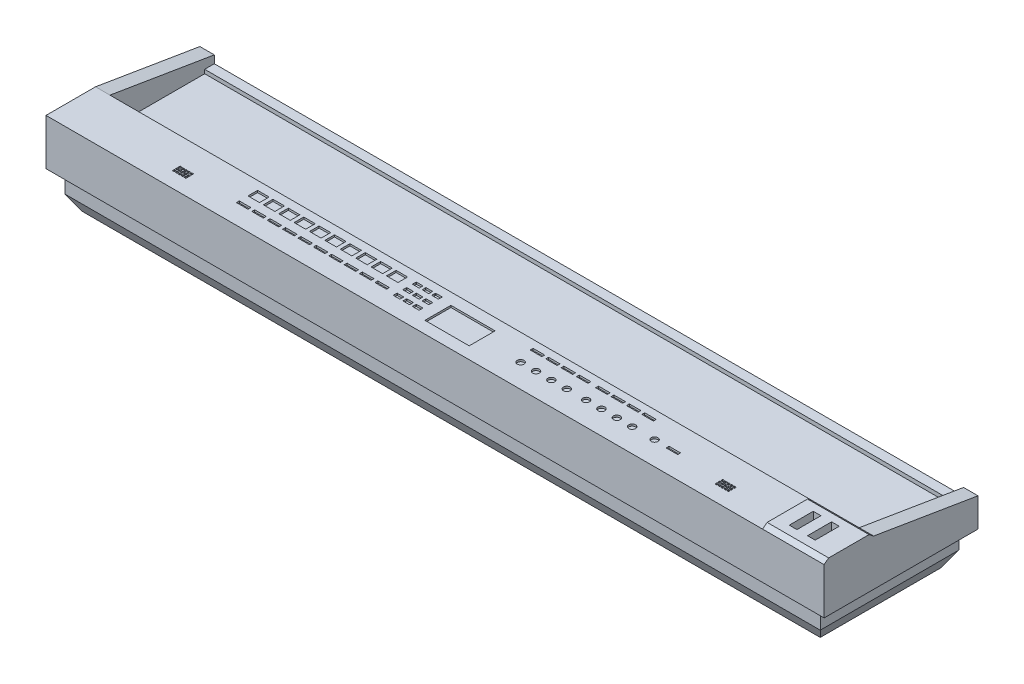
SolidWorks part; units mm, degrees
material "PE High Density"
ref_plane "Front Plane" through (0, 0, 0) normal (0, 0, 1) x (1, 0, 0)
ref_plane "Top Plane" through (0, 0, 0) normal (0, 1, 0) x (1, 0, 0)
ref_plane "Right Plane" through (0, 0, 0) normal (1, 0, 0) x (0, 0, -1)
sketch "Sketch1" plane through (0, 0, 0) normal (1, 0, 0) x (0, 0, -1)
  line L0 (0, 0) -> (0, 47.625)
  line L1 (0, 47.625) -> (-172.2712, 76.2)
  line L5 (-254, 0) -> (0, 0)
  line L7 (-254, 76.2) -> (-254, 0)
  line L9 (-254, 76.2) -> (-172.2712, 76.2)
  dimension "D1" = 47.625
  dimension "D2" = 254
  dimension "D4" = 174.625
  dimension "D6" = 76.2
extrude "Boss-Extrude1" add sketch "Sketch1" along normal blind 23.8125
sketch "Sketch2" plane through (0, 0, 0) normal (-1, 0, 0) x (0, 0, 1)
  line L0 (0, 0) -> (0, 34.925)
  line L1 (0, 0) -> (0, 47.625) construction
  line L2 (0, 34.925) -> (15.875, 34.925)
  line L3 (15.875, 34.925) -> (15.875, 28.575)
  line L4 (15.875, 28.575) -> (172.2712, 28.575)
  line L5 (172.2712, 28.575) -> (172.2712, 76.2)
  line L6 (172.2712, 76.2) -> (254, 76.2)
  line L7 (254, 76.2) -> (254, 0)
  line L8 (254, 0) -> (0, 0)
  dimension "D1" = 34.925
  dimension "D2" = 15.875
  dimension "D3" = 6.35
extrude "Boss-Extrude2" add sketch "Sketch2" along normal blind 1236.6625
sketch "Sketch3" plane through (-1236.6625, 0, 0) normal (-1, 0, 0) x (0, 0, 1)
  line L0 (0, 47.625) -> (0, 0)
  line L1 (0, 0) -> (254, 0)
  line L2 (254, 0) -> (254, 76.2)
  line L3 (254, 76.2) -> (172.2712, 76.2)
  line L4 (172.2712, 76.2) -> (0, 47.625)
extrude "Boss-Extrude3" add sketch "Sketch3" along normal blind 23.8125
sketch "Sketch4" plane through (23.8125, 0, 0) normal (1, 0, 0) x (0, 0, -1)
  line L0 (-254, 76.2) -> (-246.4731, 82.0371)
  line L1 (-172.2712, 76.2) -> (-179.7981, 82.0371)
  line L2 (-179.7981, 82.0371) -> (-246.4731, 82.0371)
  line L3 (-254, 76.2) -> (-172.2712, 76.2)
  dimension "D1" = 9.525
  dimension "D2" = 66.675
extrude "Boss-Extrude4" add sketch "Sketch4" against normal blind 101.6
ref_plane "Plane1" through (4.7625, 0, 0) normal (1, 0, 0) x (0, 0, -1)
sketch "Sketch5" plane through (4.7625, 0, 0) normal (1, 0, 0) x (0, 0, -1)
  line L0 (-241.3, 0) -> (-241.3, -33.3375)
  line L1 (-254, 0) -> (0, 0) construction
  line L2 (-241.3, -33.3375) -> (-227.0125, -58.0842)
  line L3 (-227.0125, -58.0842) -> (-26.9875, -58.0842)
  line L4 (-26.9875, -58.0842) -> (-12.7, -33.3375)
  line L5 (-12.7, -33.3375) -> (-12.7, 0)
  line L6 (-12.7, 0) -> (-241.3, 0)
  line L7 (0, 0) -> (0, 47.625) construction
  line L8 (-254, 76.2) -> (-254, 0) construction
  dimension "D1" = 33.3375
  dimension "D2" = 12.7
  dimension "D3" = 12.7
  dimension "D4" = 28.575
  dimension "D5" = 200.025
extrude "Boss-Extrude5" add sketch "Sketch5" against normal offset from surface (1246.1875 mm away) 19.05 up to face at (-1260.475, 40.005, 136.0542)
sketch "Sketch6" plane through (0, 0, 12.7) normal (0, 0, -1) x (-1, 0, 0)
  line L3 (9.525, -58.0842) -> (-4.7625, -33.3375)
  line L4 (9.525, -58.0842) -> (-4.7625, -58.0842)
  line L5 (-4.7625, -58.0842) -> (-4.7625, -33.3375)
  line L6 (618.3312, 0) -> (618.3312, -117.3939) construction
  line L7 (1241.425, 0) -> (-4.7625, 0) construction
  line L8 (1241.425, -58.0842) -> (1241.425, -33.3375)
  line L9 (1227.1375, -58.0842) -> (1241.425, -58.0842)
  line L10 (1227.1375, -58.0842) -> (1241.425, -33.3375)
  dimension "D1" = 14.2875
  dimension "D2" = 28.575
extrude "Cut-Extrude1" cut sketch "Sketch6" against normal through all
sketch "Sketch7" plane through (0, 82.0371, 0) normal (0, 1, 0) x (1, 0, 0)
  line L0 (-12.7, -192.4981) -> (-25.4, -192.4981)
  line L1 (-25.4, -192.4981) -> (-25.4, -232.1856)
  line L2 (-25.4, -232.1856) -> (-12.7, -232.1856)
  line L3 (-12.7, -232.1856) -> (-12.7, -192.4981)
  line L4 (-77.7875, -179.7981) -> (23.8125, -179.7981) construction
  line L5 (-42.8625, -192.4981) -> (-55.5625, -192.4981)
  line L6 (-42.8625, -192.4981) -> (-42.8625, -232.1856)
  line L7 (-42.8625, -232.1856) -> (-55.5625, -232.1856)
  line L8 (-55.5625, -192.4981) -> (-55.5625, -232.1856)
  line L9 (-77.7875, -254) -> (-77.7875, -172.2712) construction
  dimension "D1" = 12.7
  dimension "D2" = 12.7
  dimension "D3" = 39.6875
  dimension "D4" = 12.7
  dimension "D5" = 22.225
  dimension "D6" = 17.4625
extrude "Cut-Extrude2" cut sketch "Sketch7" against normal blind 25.7969
sketch "Sketch8" plane through (0, 76.2, 0) normal (0, 1, 0) x (1, 0, 0)
  line L0 (23.8125, -179.7981) -> (23.8125, -246.4731) construction
  line L1 (-322.2625, -184.9712) -> (-341.3125, -184.9712)
  line L2 (-322.2625, -184.9712) -> (-322.2625, -189.7337)
  line L3 (-322.2625, -189.7337) -> (-341.3125, -189.7337)
  line L4 (-341.3125, -184.9712) -> (-341.3125, -189.7337)
  line L5 (-322.2625, -184.9712) -> (-341.3125, -189.7337) construction
  line L6 (-322.2625, -189.7337) -> (-341.3125, -184.9712) construction
  line L7 (-1236.6625, -172.2712) -> (-77.7875, -172.2712) construction
  line L8 (-423.8625, -184.9712) -> (-423.8625, -243.2707) construction
  line L9 (-347.6625, -184.9712) -> (-366.7125, -184.9712)
  line L10 (-347.6625, -184.9712) -> (-347.6625, -189.7337)
  line L11 (-347.6625, -189.7337) -> (-366.7125, -189.7337)
  line L12 (-366.7125, -184.9712) -> (-366.7125, -189.7337)
  line L13 (-373.0625, -184.9712) -> (-392.1125, -184.9712)
  line L14 (-373.0625, -184.9712) -> (-373.0625, -189.7337)
  line L15 (-373.0625, -189.7337) -> (-392.1125, -189.7337)
  line L16 (-392.1125, -184.9712) -> (-392.1125, -189.7337)
  line L17 (-398.4625, -184.9712) -> (-417.5125, -184.9712)
  line L18 (-398.4625, -184.9712) -> (-398.4625, -189.7337)
  line L19 (-398.4625, -189.7337) -> (-417.5125, -189.7337)
  line L20 (-417.5125, -184.9712) -> (-417.5125, -189.7337)
  line L21 (-525.4625, -189.7337) -> (-506.4125, -184.9712) construction
  line L22 (-525.4625, -184.9712) -> (-506.4125, -189.7337) construction
  line L23 (-430.2125, -184.9712) -> (-430.2125, -189.7337)
  line L24 (-449.2625, -189.7337) -> (-430.2125, -189.7337)
  line L25 (-449.2625, -184.9712) -> (-449.2625, -189.7337)
  line L26 (-449.2625, -184.9712) -> (-430.2125, -184.9712)
  line L27 (-455.6125, -184.9712) -> (-455.6125, -189.7337)
  line L28 (-474.6625, -189.7337) -> (-455.6125, -189.7337)
  line L29 (-474.6625, -184.9712) -> (-474.6625, -189.7337)
  line L30 (-474.6625, -184.9712) -> (-455.6125, -184.9712)
  line L31 (-481.0125, -184.9712) -> (-481.0125, -189.7337)
  line L32 (-500.0625, -189.7337) -> (-481.0125, -189.7337)
  line L33 (-500.0625, -184.9712) -> (-500.0625, -189.7337)
  line L34 (-500.0625, -184.9712) -> (-481.0125, -184.9712)
  line L35 (-506.4125, -184.9712) -> (-506.4125, -189.7337)
  line L36 (-525.4625, -189.7337) -> (-506.4125, -189.7337)
  line L37 (-525.4625, -184.9712) -> (-525.4625, -189.7337)
  line L38 (-525.4625, -184.9712) -> (-506.4125, -184.9712)
  line L39 (-313.3725, -182.6085) -> (-313.3725, -245.3051) construction
  line L41 (-254.3175, -212.7524) -> (-273.3675, -212.7524)
  line L42 (-254.3175, -212.7524) -> (-254.3175, -217.5149)
  line L43 (-254.3175, -217.5149) -> (-273.3675, -217.5149)
  line L44 (-273.3675, -212.7524) -> (-273.3675, -217.5149)
  line L45 (-254.3175, -212.7524) -> (-273.3675, -217.5149) construction
  line L46 (-254.3175, -217.5149) -> (-273.3675, -212.7524) construction
  circle A0 centre (-331.7875, -215.1337) radius 5.5562
  circle A1 centre (-357.1875, -215.1337) radius 5.5562
  circle A2 centre (-382.5875, -215.1337) radius 5.5562
  circle A3 centre (-407.9875, -215.1337) radius 5.5562
  circle A4 centre (-439.7375, -215.1337) radius 5.5562
  circle A5 centre (-465.1375, -215.1337) radius 5.5562
  circle A6 centre (-490.5375, -215.1337) radius 5.5562
  circle A7 centre (-515.9375, -215.1337) radius 5.5563
  circle A8 centre (-294.9575, -215.1337) radius 5.5562
  point P0 (-331.7875, -187.3524)
  point P26 (-357.1875, -189.7337)
  point P30 (-382.5875, -189.7337)
  point P31 (-417.5125, -187.3524)
  point P32 (-407.9875, -189.7337)
  point P59 (-515.9375, -187.3524)
  point P64 (-263.8425, -215.1337)
  point P69 (-273.3675, -215.1337)
  dimension "D11" = 11.1125
  dimension "D1" = 355.6
  dimension "D2" = 19.05
  dimension "D3" = 4.7625
  dimension "D4" = 12.7
  dimension "D5" = 19.05
  dimension "D6" = 6.35
  dimension "D7" = 6.35
  dimension "D8" = 19.05
  dimension "D9" = 19.05
  dimension "D10" = 6.35
  dimension "D12" = 25.4
  dimension "D13" = 6.35
  dimension "D14" = 8.89
  dimension "D15" = 19.05
  dimension "D16" = 4.7625
  dimension "D17" = 21.59
extrude "Cut-Extrude3" cut sketch "Sketch8" against normal blind 3.175
sketch "Sketch9" plane through (0, 76.2, 0) normal (0, 1, 0) x (1, 0, 0)
  line L1 (-581.8188, -191.3212) -> (-654.8438, -191.3212)
  line L2 (-581.8188, -191.3212) -> (-581.8187, -234.1837)
  line L3 (-581.8187, -234.1837) -> (-654.8438, -234.1837)
  line L4 (-654.8438, -191.3212) -> (-654.8438, -234.1837)
  line L5 (-581.8188, -191.3212) -> (-654.8438, -234.1837) construction
  line L6 (-581.8187, -234.1837) -> (-654.8438, -191.3212) construction
  line L7 (-1236.6625, -172.2712) -> (0, -172.2712) construction
  line L8 (-1236.6625, -172.2712) -> (-77.7875, -172.2712) construction
  point P0 (-618.3312, -212.7524)
  point P10 (-618.3312, -172.2712)
  dimension "D1" = 42.8625
  dimension "D2" = 19.05
  dimension "D3" = 73.025
extrude "Cut-Extrude4" cut sketch "Sketch9" against normal blind 3.175
sketch "Sketch10" plane through (0, 76.2, 0) normal (0, 1, 0) x (1, 0, 0)
  line L0 (-654.8438, -191.3212) -> (-654.8438, -234.1837) construction
  line L1 (-673.8937, -186.5587) -> (-685.0062, -186.5587)
  line L2 (-673.8937, -186.5587) -> (-673.8937, -192.9087)
  line L3 (-673.8937, -192.9087) -> (-685.0062, -192.9087)
  line L4 (-685.0062, -186.5587) -> (-685.0062, -192.9087)
  line L5 (-1236.6625, -172.2712) -> (0, -172.2712) construction
  line L6 (-660.8342, -197.6712) -> (-722.2414, -197.6712) construction
  line L7 (-689.7687, -186.5587) -> (-700.8812, -186.5587)
  line L8 (-689.7687, -186.5587) -> (-689.7687, -192.9087)
  line L9 (-689.7687, -192.9087) -> (-700.8812, -192.9087)
  line L10 (-700.8812, -186.5587) -> (-700.8812, -192.9087)
  line L11 (-705.6437, -186.5587) -> (-716.7562, -186.5587)
  line L12 (-705.6437, -186.5587) -> (-705.6437, -192.9087)
  line L13 (-705.6437, -192.9087) -> (-716.7562, -192.9087)
  line L14 (-716.7562, -186.5587) -> (-716.7562, -192.9087)
  line L15 (-716.7562, -208.7837) -> (-716.7562, -202.4337)
  line L16 (-705.6437, -202.4337) -> (-716.7562, -202.4337)
  line L17 (-705.6437, -208.7837) -> (-705.6437, -202.4337)
  line L18 (-705.6437, -208.7837) -> (-716.7562, -208.7837)
  line L19 (-700.8812, -208.7837) -> (-700.8812, -202.4337)
  line L20 (-689.7687, -202.4337) -> (-700.8812, -202.4337)
  line L21 (-689.7687, -208.7837) -> (-689.7687, -202.4337)
  line L22 (-689.7687, -208.7837) -> (-700.8812, -208.7837)
  line L23 (-685.0062, -208.7837) -> (-685.0062, -202.4337)
  line L24 (-673.8937, -202.4337) -> (-685.0062, -202.4337)
  line L25 (-673.8937, -208.7837) -> (-673.8937, -202.4337)
  line L26 (-673.8937, -208.7837) -> (-685.0062, -208.7837)
  line L27 (-660.8342, -213.5462) -> (-722.2414, -213.5462) construction
  line L28 (-673.8937, -218.3087) -> (-685.0062, -218.3087)
  line L29 (-673.8937, -218.3087) -> (-673.8937, -224.6587)
  line L30 (-673.8937, -224.6587) -> (-685.0062, -224.6587)
  line L31 (-685.0062, -218.3087) -> (-685.0062, -224.6587)
  line L32 (-689.7687, -218.3087) -> (-700.8812, -218.3087)
  line L33 (-689.7687, -218.3087) -> (-689.7687, -224.6587)
  line L34 (-689.7687, -224.6587) -> (-700.8812, -224.6587)
  line L35 (-700.8812, -218.3087) -> (-700.8812, -224.6587)
  line L36 (-705.6437, -218.3087) -> (-716.7562, -218.3087)
  line L37 (-705.6437, -218.3087) -> (-705.6437, -224.6587)
  line L38 (-705.6437, -224.6587) -> (-716.7562, -224.6587)
  line L39 (-716.7562, -218.3087) -> (-716.7562, -224.6587)
  dimension "D1" = 19.05
  dimension "D2" = 11.1125
  dimension "D3" = 14.2875
  dimension "D4" = 6.35
  dimension "D5" = 4.7625
  dimension "D6" = 4.7625
  dimension "D7" = 9.525
  dimension "D8" = 9.525
extrude "Cut-Extrude5" cut sketch "Sketch10" against normal blind 3.175
sketch "Sketch11" plane through (0, 76.2, 0) normal (0, 1, 0) x (1, 0, 0)
  line L0 (-705.6437, -186.5587) -> (-716.7562, -186.5587) construction
  line L1 (-731.0437, -186.5587) -> (-750.0937, -186.5587)
  line L2 (-731.0437, -186.5587) -> (-731.0437, -202.4337)
  line L3 (-731.0437, -202.4337) -> (-750.0937, -202.4337)
  line L4 (-750.0937, -186.5587) -> (-750.0937, -202.4337)
  line L5 (-716.7562, -186.5587) -> (-716.7562, -192.9087) construction
  line L6 (-525.4625, -184.9712) -> (-525.4625, -189.7337) construction
  line L7 (-731.0437, -216.7212) -> (-750.0937, -216.7212)
  line L8 (-731.0437, -216.7212) -> (-731.0437, -221.4837)
  line L9 (-731.0437, -221.4837) -> (-750.0937, -221.4837)
  line L10 (-750.0937, -216.7212) -> (-750.0937, -221.4837)
  line L11 (-481.0125, -184.9712) -> (-500.0625, -184.9712) construction
  line L12 (-705.6437, -218.3087) -> (-716.7562, -218.3087) construction
  line L13 (-753.2687, -182.2074) -> (-753.2687, -235.3142) construction
  line L14 (-756.4438, -216.7212) -> (-756.4438, -221.4837)
  line L15 (-775.4937, -221.4837) -> (-756.4438, -221.4837)
  line L16 (-775.4937, -216.7212) -> (-775.4937, -221.4837)
  line L17 (-775.4937, -216.7212) -> (-756.4438, -216.7212)
  line L18 (-756.4438, -186.5587) -> (-756.4438, -202.4337)
  line L19 (-775.4937, -202.4337) -> (-756.4438, -202.4337)
  line L20 (-775.4937, -186.5587) -> (-775.4937, -202.4337)
  line L21 (-775.4937, -186.5587) -> (-756.4438, -186.5587)
  line L22 (-778.6688, -235.3142) -> (-778.6688, -182.2074) construction
  line L23 (-781.8438, -186.5587) -> (-800.8938, -186.5587)
  line L24 (-781.8438, -186.5587) -> (-781.8438, -202.4337)
  line L25 (-781.8438, -202.4337) -> (-800.8938, -202.4337)
  line L26 (-800.8938, -186.5587) -> (-800.8938, -202.4337)
  line L27 (-781.8438, -216.7212) -> (-800.8938, -216.7212)
  line L28 (-781.8438, -216.7212) -> (-781.8438, -221.4837)
  line L29 (-781.8438, -221.4837) -> (-800.8938, -221.4837)
  line L30 (-800.8938, -216.7212) -> (-800.8938, -221.4837)
  line L31 (-807.2438, -216.7212) -> (-807.2438, -221.4837)
  line L32 (-826.2938, -221.4837) -> (-807.2438, -221.4837)
  line L33 (-826.2938, -216.7212) -> (-826.2938, -221.4837)
  line L34 (-826.2938, -216.7212) -> (-807.2438, -216.7212)
  line L35 (-807.2438, -186.5587) -> (-807.2438, -202.4337)
  line L36 (-826.2938, -202.4337) -> (-807.2438, -202.4337)
  line L37 (-826.2938, -186.5587) -> (-826.2938, -202.4337)
  line L38 (-826.2938, -186.5587) -> (-807.2438, -186.5587)
  line L39 (-829.4688, -235.3142) -> (-829.4688, -182.2074) construction
  line L40 (-832.6438, -186.5587) -> (-851.6938, -186.5587)
  line L41 (-832.6438, -186.5587) -> (-832.6438, -202.4337)
  line L42 (-832.6438, -202.4337) -> (-851.6938, -202.4337)
  line L43 (-851.6938, -186.5587) -> (-851.6938, -202.4337)
  line L44 (-832.6438, -216.7212) -> (-851.6938, -216.7212)
  line L45 (-832.6438, -216.7212) -> (-832.6438, -221.4837)
  line L46 (-832.6438, -221.4837) -> (-851.6938, -221.4837)
  line L47 (-851.6938, -216.7212) -> (-851.6938, -221.4837)
  line L48 (-858.0438, -216.7212) -> (-858.0438, -221.4837)
  line L49 (-877.0938, -221.4837) -> (-858.0438, -221.4837)
  line L50 (-877.0938, -216.7212) -> (-877.0938, -221.4837)
  line L51 (-877.0938, -216.7212) -> (-858.0438, -216.7212)
  line L52 (-858.0438, -186.5587) -> (-858.0438, -202.4337)
  line L53 (-877.0938, -202.4337) -> (-858.0438, -202.4337)
  line L54 (-877.0938, -186.5587) -> (-877.0938, -202.4337)
  line L55 (-877.0938, -186.5587) -> (-858.0438, -186.5587)
  line L56 (-883.4438, -186.5587) -> (-902.4938, -186.5587)
  line L57 (-883.4438, -186.5587) -> (-883.4438, -202.4337)
  line L58 (-883.4438, -202.4337) -> (-902.4938, -202.4337)
  line L59 (-902.4938, -186.5587) -> (-902.4938, -202.4337)
  line L60 (-883.4438, -216.7212) -> (-902.4938, -216.7212)
  line L61 (-883.4438, -216.7212) -> (-883.4438, -221.4837)
  line L62 (-883.4438, -221.4837) -> (-902.4938, -221.4837)
  line L63 (-902.4938, -216.7212) -> (-902.4938, -221.4837)
  line L64 (-908.8438, -216.7212) -> (-908.8438, -221.4837)
  line L65 (-927.8938, -221.4837) -> (-908.8438, -221.4837)
  line L66 (-927.8938, -216.7212) -> (-927.8938, -221.4837)
  line L67 (-927.8938, -216.7212) -> (-908.8438, -216.7212)
  line L68 (-908.8438, -186.5587) -> (-908.8438, -202.4337)
  line L69 (-927.8938, -202.4337) -> (-908.8438, -202.4337)
  line L70 (-927.8938, -186.5587) -> (-927.8938, -202.4337)
  line L71 (-927.8938, -186.5587) -> (-908.8438, -186.5587)
  line L72 (-931.0688, -235.3142) -> (-931.0688, -182.2074) construction
  line L73 (-934.2438, -186.5587) -> (-953.2938, -186.5587)
  line L74 (-934.2438, -186.5587) -> (-934.2438, -202.4337)
  line L75 (-934.2438, -202.4337) -> (-953.2938, -202.4337)
  line L76 (-953.2938, -186.5587) -> (-953.2938, -202.4337)
  line L77 (-934.2438, -216.7212) -> (-953.2938, -216.7212)
  line L78 (-934.2438, -216.7212) -> (-934.2438, -221.4837)
  line L79 (-934.2438, -221.4837) -> (-953.2938, -221.4837)
  line L80 (-953.2938, -216.7212) -> (-953.2938, -221.4837)
  line L81 (-959.6438, -216.7212) -> (-959.6438, -221.4837)
  line L82 (-978.6938, -221.4837) -> (-959.6438, -221.4837)
  line L83 (-978.6938, -216.7212) -> (-978.6938, -221.4837)
  line L84 (-978.6938, -216.7212) -> (-959.6438, -216.7212)
  line L85 (-959.6438, -186.5587) -> (-959.6438, -202.4337)
  line L86 (-978.6938, -202.4337) -> (-959.6438, -202.4337)
  line L87 (-978.6938, -186.5587) -> (-978.6938, -202.4337)
  line L88 (-978.6938, -186.5587) -> (-959.6438, -186.5587)
  dimension "D1" = 15.875
  dimension "D2" = 19.05
  dimension "D3" = 14.2875
  dimension "D4" = 1.5875
  dimension "D5" = 3.175
  dimension "D6" = 3.175
  dimension "D7" = 3.175
  dimension "D8" = 3.175
extrude "Cut-Extrude6" cut sketch "Sketch11" against normal blind 3.175
sketch "Sketch12" plane through (0, 76.2, 0) normal (0, 1, 0) x (1, 0, 0)
  line L0 (23.8125, -179.7981) -> (23.8125, -246.4731) construction
  line L1 (-159.385, -215.9) -> (-162.56, -215.9)
  line L2 (-159.385, -215.9) -> (-159.385, -219.075)
  line L3 (-159.385, -219.075) -> (-162.56, -219.075)
  line L4 (-162.56, -215.9) -> (-162.56, -219.075)
  line L5 (-159.385, -220.6625) -> (-162.56, -220.6625)
  line L6 (-159.385, -220.6625) -> (-159.385, -223.8375)
  line L7 (-159.385, -223.8375) -> (-162.56, -223.8375)
  line L8 (-162.56, -220.6625) -> (-162.56, -223.8375)
  line L9 (-159.385, -225.425) -> (-162.56, -225.425)
  line L10 (-159.385, -225.425) -> (-159.385, -228.6)
  line L11 (-159.385, -228.6) -> (-162.56, -228.6)
  line L12 (-162.56, -225.425) -> (-162.56, -228.6)
  line L13 (-164.1475, -215.9) -> (-167.3225, -215.9)
  line L14 (-164.1475, -215.9) -> (-164.1475, -219.075)
  line L15 (-164.1475, -219.075) -> (-167.3225, -219.075)
  line L16 (-167.3225, -215.9) -> (-167.3225, -219.075)
  line L17 (-168.91, -215.9) -> (-172.085, -215.9)
  line L18 (-168.91, -215.9) -> (-168.91, -219.075)
  line L19 (-168.91, -219.075) -> (-172.085, -219.075)
  line L20 (-172.085, -215.9) -> (-172.085, -219.075)
  line L21 (-173.6725, -215.9) -> (-176.8475, -215.9)
  line L22 (-173.6725, -215.9) -> (-173.6725, -219.075)
  line L23 (-173.6725, -219.075) -> (-176.8475, -219.075)
  line L24 (-176.8475, -215.9) -> (-176.8475, -219.075)
  line L25 (-178.435, -215.9) -> (-181.61, -215.9)
  line L26 (-178.435, -215.9) -> (-178.435, -219.075)
  line L27 (-178.435, -219.075) -> (-181.61, -219.075)
  line L28 (-181.61, -215.9) -> (-181.61, -219.075)
  line L29 (-164.1475, -220.6625) -> (-167.3225, -220.6625)
  line L30 (-164.1475, -220.6625) -> (-164.1475, -223.8375)
  line L31 (-164.1475, -223.8375) -> (-167.3225, -223.8375)
  line L32 (-167.3225, -220.6625) -> (-167.3225, -223.8375)
  line L33 (-168.91, -220.6625) -> (-172.085, -220.6625)
  line L34 (-168.91, -220.6625) -> (-168.91, -223.8375)
  line L35 (-168.91, -223.8375) -> (-172.085, -223.8375)
  line L36 (-172.085, -220.6625) -> (-172.085, -223.8375)
  line L37 (-173.6725, -220.6625) -> (-176.8475, -220.6625)
  line L38 (-173.6725, -220.6625) -> (-173.6725, -223.8375)
  line L39 (-173.6725, -223.8375) -> (-176.8475, -223.8375)
  line L40 (-176.8475, -220.6625) -> (-176.8475, -223.8375)
  line L41 (-178.435, -220.6625) -> (-181.61, -220.6625)
  line L42 (-178.435, -220.6625) -> (-178.435, -223.8375)
  line L43 (-178.435, -223.8375) -> (-181.61, -223.8375)
  line L44 (-181.61, -220.6625) -> (-181.61, -223.8375)
  line L45 (-164.1475, -225.425) -> (-167.3225, -225.425)
  line L46 (-164.1475, -225.425) -> (-164.1475, -228.6)
  line L47 (-164.1475, -228.6) -> (-167.3225, -228.6)
  line L48 (-167.3225, -225.425) -> (-167.3225, -228.6)
  line L49 (-168.91, -225.425) -> (-172.085, -225.425)
  line L50 (-168.91, -225.425) -> (-168.91, -228.6)
  line L51 (-168.91, -228.6) -> (-172.085, -228.6)
  line L52 (-172.085, -225.425) -> (-172.085, -228.6)
  line L53 (-173.6725, -225.425) -> (-176.8475, -225.425)
  line L54 (-173.6725, -225.425) -> (-173.6725, -228.6)
  line L55 (-173.6725, -228.6) -> (-176.8475, -228.6)
  line L56 (-176.8475, -225.425) -> (-176.8475, -228.6)
  line L57 (-178.435, -225.425) -> (-181.61, -225.425)
  line L58 (-178.435, -225.425) -> (-178.435, -228.6)
  line L59 (-178.435, -228.6) -> (-181.61, -228.6)
  line L60 (-181.61, -225.425) -> (-181.61, -228.6)
  line L61 (-77.7875, -254) -> (-1260.475, -254) construction
  line L62 (-618.3312, -172.2712) -> (-618.3312, -332.4025) construction
  line L63 (-1236.6625, -172.2712) -> (0, -172.2712) construction
  line L64 (-1055.0525, -225.425) -> (-1055.0525, -228.6)
  line L65 (-1058.2275, -228.6) -> (-1055.0525, -228.6)
  line L66 (-1058.2275, -225.425) -> (-1058.2275, -228.6)
  line L67 (-1058.2275, -225.425) -> (-1055.0525, -225.425)
  line L68 (-1059.815, -225.425) -> (-1059.815, -228.6)
  line L69 (-1062.99, -228.6) -> (-1059.815, -228.6)
  line L70 (-1062.99, -225.425) -> (-1062.99, -228.6)
  line L71 (-1062.99, -225.425) -> (-1059.815, -225.425)
  line L72 (-1064.5775, -225.425) -> (-1064.5775, -228.6)
  line L73 (-1067.7525, -228.6) -> (-1064.5775, -228.6)
  line L74 (-1067.7525, -225.425) -> (-1067.7525, -228.6)
  line L75 (-1067.7525, -225.425) -> (-1064.5775, -225.425)
  line L76 (-1069.34, -225.425) -> (-1069.34, -228.6)
  line L77 (-1072.515, -228.6) -> (-1069.34, -228.6)
  line L78 (-1072.515, -225.425) -> (-1072.515, -228.6)
  line L79 (-1072.515, -225.425) -> (-1069.34, -225.425)
  line L80 (-1055.0525, -220.6625) -> (-1055.0525, -223.8375)
  line L81 (-1058.2275, -223.8375) -> (-1055.0525, -223.8375)
  line L82 (-1058.2275, -220.6625) -> (-1058.2275, -223.8375)
  line L83 (-1058.2275, -220.6625) -> (-1055.0525, -220.6625)
  line L84 (-1059.815, -220.6625) -> (-1059.815, -223.8375)
  line L85 (-1062.99, -223.8375) -> (-1059.815, -223.8375)
  line L86 (-1062.99, -220.6625) -> (-1062.99, -223.8375)
  line L87 (-1062.99, -220.6625) -> (-1059.815, -220.6625)
  line L88 (-1064.5775, -220.6625) -> (-1064.5775, -223.8375)
  line L89 (-1067.7525, -223.8375) -> (-1064.5775, -223.8375)
  line L90 (-1067.7525, -220.6625) -> (-1067.7525, -223.8375)
  line L91 (-1067.7525, -220.6625) -> (-1064.5775, -220.6625)
  line L92 (-1069.34, -220.6625) -> (-1069.34, -223.8375)
  line L93 (-1072.515, -223.8375) -> (-1069.34, -223.8375)
  line L94 (-1072.515, -220.6625) -> (-1072.515, -223.8375)
  line L95 (-1072.515, -220.6625) -> (-1069.34, -220.6625)
  line L96 (-1055.0525, -215.9) -> (-1055.0525, -219.075)
  line L97 (-1058.2275, -219.075) -> (-1055.0525, -219.075)
  line L98 (-1058.2275, -215.9) -> (-1058.2275, -219.075)
  line L99 (-1058.2275, -215.9) -> (-1055.0525, -215.9)
  line L100 (-1059.815, -215.9) -> (-1059.815, -219.075)
  line L101 (-1062.99, -219.075) -> (-1059.815, -219.075)
  line L102 (-1062.99, -215.9) -> (-1062.99, -219.075)
  line L103 (-1062.99, -215.9) -> (-1059.815, -215.9)
  line L104 (-1064.5775, -215.9) -> (-1064.5775, -219.075)
  line L105 (-1067.7525, -219.075) -> (-1064.5775, -219.075)
  line L106 (-1067.7525, -215.9) -> (-1067.7525, -219.075)
  line L107 (-1067.7525, -215.9) -> (-1064.5775, -215.9)
  line L108 (-1069.34, -215.9) -> (-1069.34, -219.075)
  line L109 (-1072.515, -219.075) -> (-1069.34, -219.075)
  line L110 (-1072.515, -215.9) -> (-1072.515, -219.075)
  line L111 (-1072.515, -215.9) -> (-1069.34, -215.9)
  line L112 (-1074.1025, -225.425) -> (-1074.1025, -228.6)
  line L113 (-1077.2775, -228.6) -> (-1074.1025, -228.6)
  line L114 (-1077.2775, -225.425) -> (-1077.2775, -228.6)
  line L115 (-1077.2775, -225.425) -> (-1074.1025, -225.425)
  line L116 (-1074.1025, -220.6625) -> (-1074.1025, -223.8375)
  line L117 (-1077.2775, -223.8375) -> (-1074.1025, -223.8375)
  line L118 (-1077.2775, -220.6625) -> (-1077.2775, -223.8375)
  line L119 (-1077.2775, -220.6625) -> (-1074.1025, -220.6625)
  line L120 (-1074.1025, -215.9) -> (-1074.1025, -219.075)
  line L121 (-1077.2775, -219.075) -> (-1074.1025, -219.075)
  line L122 (-1077.2775, -215.9) -> (-1077.2775, -219.075)
  line L123 (-1077.2775, -215.9) -> (-1074.1025, -215.9)
  point P60 (-170.4975, -215.9)
  dimension "D1" = 3.175
  dimension "D2" = 3.175
  dimension "D3" = 1.5875
  dimension "D4" = 1.5875
  dimension "D5" = 1.5875
  dimension "D6" = 1.5875
  dimension "D7" = 1.5875
  dimension "D8" = 1.5875
  dimension "D9" = 194.31
  dimension "D10" = 25.4
extrude "Cut-Extrude7" cut sketch "Sketch12" against normal blind 6.35
fillet "Fillet1" radius 0.635 36 edges at (-705.6437, 74.6125, 186.5587) (-689.7687, 74.6125, 186.5587) (-689.7687, 74.6125, 202.4337) (-705.6437, 74.6125, 202.4337) (-705.6437, 74.6125, 218.3087) (-689.7687, 74.6125, 218.3087) (-700.8812, 74.6125, 208.7837) (-700.8812, 74.6125, 192.9087) (-716.7562, 74.6125, 192.9087) (-716.7562, 74.6125, 208.7837) (-716.7562, 74.6125, 224.6587) (-700.8812, 74.6125, 224.6587) (-705.6437, 74.6125, 224.6587) (-689.7687, 74.6125, 224.6587) (-689.7687, 74.6125, 208.7837) (-705.6437, 74.6125, 208.7837) (-705.6437, 74.6125, 192.9087) (-689.7687, 74.6125, 192.9087) (-716.7562, 74.6125, 218.3087) (-700.8812, 74.6125, 218.3087) (-716.7562, 74.6125, 202.4337) (-700.8812, 74.6125, 202.4337) (-716.7562, 74.6125, 186.5587) (-700.8812, 74.6125, 186.5587) (-685.0062, 74.6125, 186.5587) (-685.0062, 74.6125, 192.9087) (-673.8937, 74.6125, 192.9087) (-673.8937, 74.6125, 186.5587) (-673.8937, 74.6125, 202.4337) (-685.0062, 74.6125, 202.4337) (-685.0062, 74.6125, 208.7837) (-673.8937, 74.6125, 208.7837) (-685.0062, 74.6125, 218.3087) (-673.8937, 74.6125, 218.3087) (-673.8937, 74.6125, 224.6587) (-685.0062, 74.6125, 224.6587)
